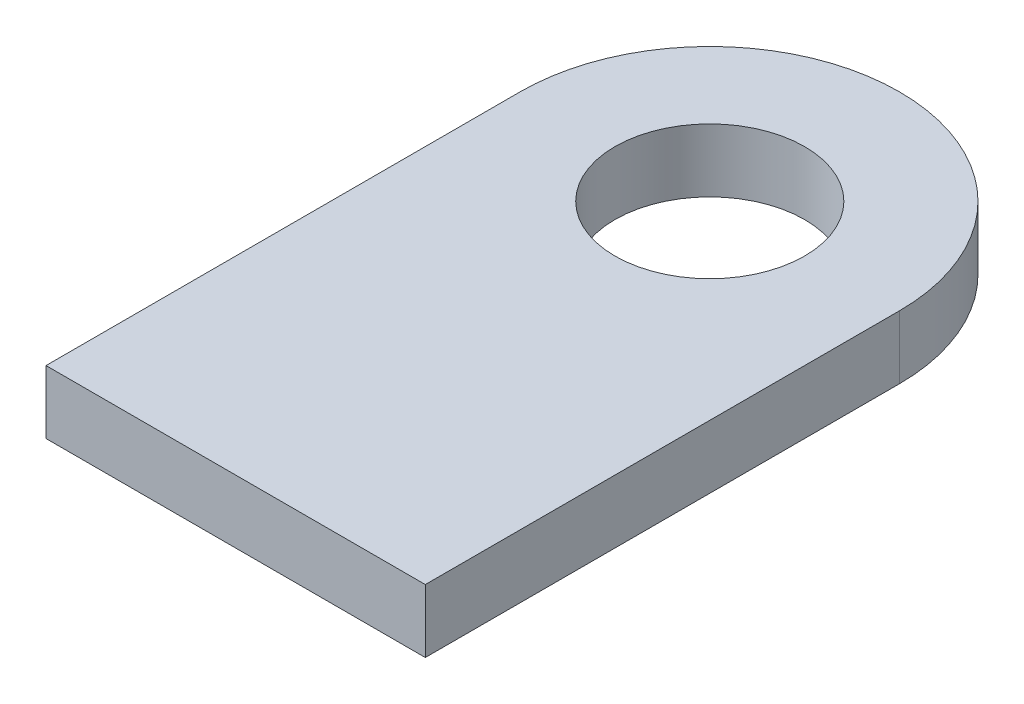
SolidWorks part; units mm, degrees
ref_plane "Płaszczyzna przednia" through (0, 0, 0) normal (0, 0, 1) x (1, 0, 0)
ref_plane "Płaszczyzna górna" through (0, 0, 0) normal (0, 1, 0) x (1, 0, 0)
ref_plane "Płaszczyzna prawa" through (0, 0, 0) normal (1, 0, 0) x (0, 0, -1)
sketch "Szkic1" plane through (0, 0, 0) normal (0, 1, 0) x (1, 0, 0)
  line L0 (-6, 0) -> (-6, -15)
  line L1 (6, 0) -> (6, -15)
  line L2 (6, -15) -> (-6, -15)
  arc A1 (-6, 0) -> (6, 0) centre (0, 0) cw
  dimension "D3" = 6
  dimension "D2" = 15
extrude "Dodanie-wyciągnięcie1" add sketch "Szkic1" along normal blind 2
hole_wizard "Otwór1" positions "Szkic2" profile "Szkic3" legacy end condition up to next
sketch "Szkic2" plane through (0, 2, 0) normal (0, 1, 0) x (1, 0, 0)
  point P0 (0, 0)
sketch "Szkic3" plane through (0, 2, 0) normal (1, 0, 0) x (0, 0, 1)
  line L0 (0, 0) -> (0, 2)
  line L1 (0, 2) -> (3, 2)
  line L2 (3, 2) -> (3, 0)
  line L3 (3, 0) -> (0, 0)
  line L4 (0, 110) -> (0, -10) construction
  dimension "Średnica" = 6
  dimension "Głębokość" = 2
